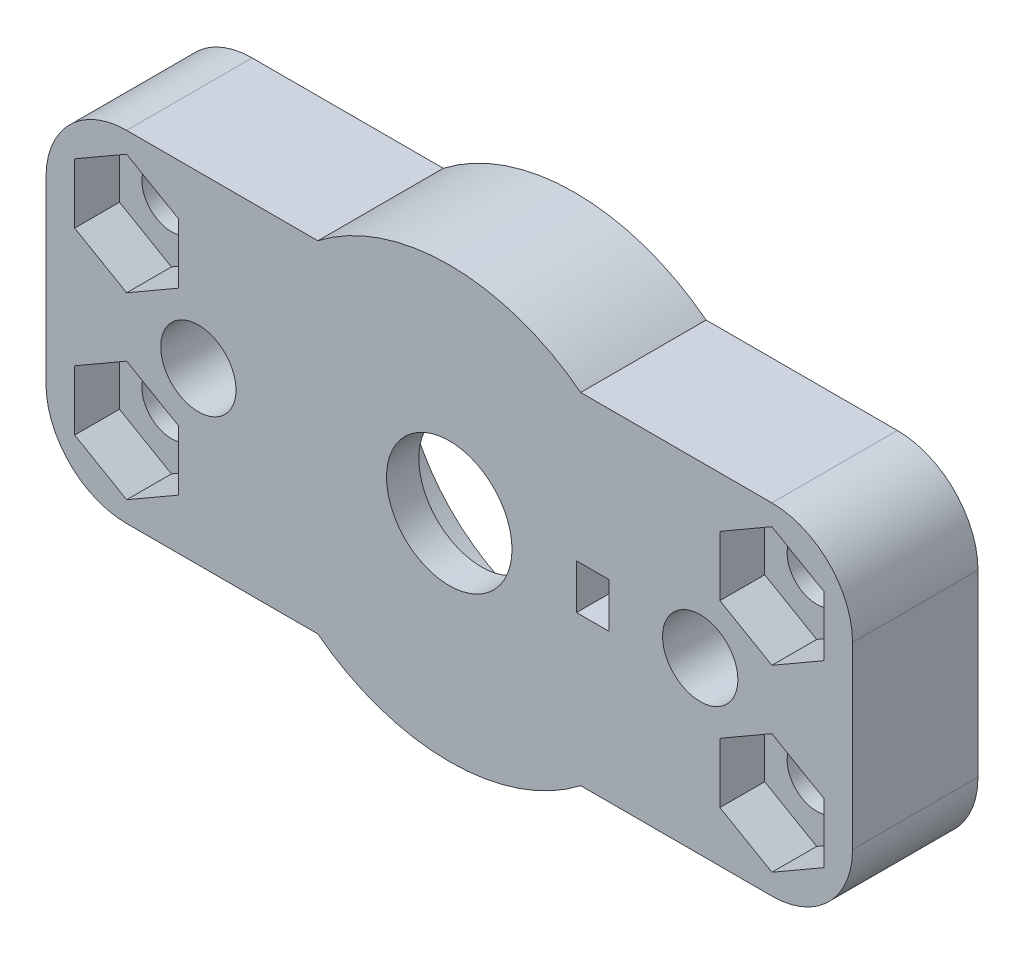
SolidWorks part; units mm, degrees
ref_plane "Front Plane" through (0, 0, 0) normal (0, 0, 1) x (1, 0, 0)
ref_plane "Top Plane" through (0, 0, 0) normal (0, 1, 0) x (1, 0, 0)
ref_plane "Right Plane" through (0, 0, 0) normal (1, 0, 0) x (0, 0, -1)
sketch "Sketch1" plane through (0, 0, 0) normal (0, 0, 1) x (1, 0, 0)
  circle A0 centre (0, 0) radius 9.5 construction
  circle A1 centre (0, 0) radius 2.5 construction
  dimension "D1" = 19
  dimension "D2" = 5
sketch "Sketch2" plane through (0, 0, 0) normal (0, 0, 1) x (1, 0, 0)
  line L0 (-18, 9.5) -> (-7.3314, 9.5)
  line L5 (0, 0) -> (0, 12) construction
  line L6 (0, 0) -> (-30.5723, 0) construction
  line L7 (-22.5, 5) -> (-22.5, -5)
  line L8 (22.5, 5) -> (22.5, -5)
  line L9 (18, 9.5) -> (7.3314, 9.5)
  line L10 (18, -9.5) -> (7.3314, -9.5)
  line L11 (-18, -9.5) -> (-7.3314, -9.5)
  arc A1 (-7.3314, 9.5) -> (7.3314, 9.5) centre (0, 0) cw
  circle A3 centre (0, 0) radius 9.5 construction
  arc A4 (-7.3314, -9.5) -> (7.3314, -9.5) centre (0, 0) ccw
  arc A5 (22.5, 5) -> (18, 9.5) centre (18, 5) ccw
  arc A6 (18, -9.5) -> (22.5, -5) centre (18, -5) ccw
  arc A7 (-22.5, -5) -> (-18, -9.5) centre (-18, -5) ccw
  arc A8 (-22.5, 5) -> (-18, 9.5) centre (-18, 5) cw
  circle A10 centre (-18, 5) radius 1.65
  circle A11 centre (18, 5) radius 1.65
  circle A12 centre (18, -5) radius 1.65
  circle A13 centre (-18, -5) radius 1.65
  point P0 (0, 0)
  point P8 (22.5, 9.5)
  point P21 (22.5, 0)
  point P22 (-22.5, 0)
  point P23 (22.5, -9.5)
  point P26 (-22.5, -9.5)
  point P29 (-22.5, 9.5)
  dimension "D1" = 2.5
  dimension "D2" = 4.5
  dimension "D3" = 3.3
  dimension "D4" = 10
  dimension "D5" = 45
extrude "Boss-Extrude1" add sketch "Sketch2" along normal blind 7
sketch "Sketch3" plane through (0, 0, 0) normal (0, 0, 1) x (1, 0, 0)
  circle A3 centre (0, 0) radius 9.7
  circle A4 centre (0, 0) radius 9.7
  dimension "D1" = 0.2
extrude "Cut-Extrude1" cut sketch "Sketch3" along normal blind 5
sketch "Sketch4" plane through (0, 0, 5) normal (0, 0, -1) x (-1, 0, 0)
  circle A0 centre (0, 0) radius 7.5
  dimension "D1" = 15
extrude "Cut-Extrude2" cut sketch "Sketch4" against normal blind 5
sketch "Sketch5" plane through (0, 0, 7) normal (0, 0, 1) x (1, 0, 0)
  line L0 (0, 0) -> (0, 12) construction
  line L1 (-18, 8.3486) -> (-20.9, 6.6743)
  line L2 (-20.9, 6.6743) -> (-20.9, 3.3257)
  line L3 (-20.9, 3.3257) -> (-18, 1.6514)
  line L4 (-18, 1.6514) -> (-15.1, 3.3257)
  line L5 (-15.1, 3.3257) -> (-15.1, 6.6743)
  line L6 (-15.1, 6.6743) -> (-18, 8.3486)
  line L7 (15.1, 6.6743) -> (18, 8.3486)
  line L8 (-22.5, 5) -> (-22.5, -5) construction
  line L9 (-22.5, 0) -> (0, 0) construction
  line L10 (15.1, 3.3257) -> (15.1, 6.6743)
  line L11 (18, 1.6514) -> (15.1, 3.3257)
  line L12 (20.9, 3.3257) -> (18, 1.6514)
  line L13 (20.9, 6.6743) -> (20.9, 3.3257)
  line L14 (18, 8.3486) -> (20.9, 6.6743)
  line L15 (15.1, -3.3257) -> (15.1, -6.6743)
  line L16 (18, -1.6514) -> (15.1, -3.3257)
  line L17 (20.9, -3.3257) -> (18, -1.6514)
  line L18 (20.9, -6.6743) -> (20.9, -3.3257)
  line L19 (18, -8.3486) -> (20.9, -6.6743)
  line L20 (15.1, -6.6743) -> (18, -8.3486)
  line L21 (-15.1, -6.6743) -> (-18, -8.3486)
  line L22 (-15.1, -3.3257) -> (-15.1, -6.6743)
  line L23 (-18, -1.6514) -> (-15.1, -3.3257)
  line L24 (-20.9, -3.3257) -> (-18, -1.6514)
  line L25 (-20.9, -6.6743) -> (-20.9, -3.3257)
  line L26 (-18, -8.3486) -> (-20.9, -6.6743)
  circle A0 centre (-18, 5) radius 2.9 construction
  arc A1 (7.3314, 9.5) -> (-7.3314, 9.5) centre (0, 0) ccw construction
  dimension "D1" = 5.8
extrude "Cut-Extrude3" cut sketch "Sketch5" against normal blind 2.5
sketch "Sketch6" plane through (0, 0, 7) normal (0, 0, 1) x (1, 0, 0)
  circle A0 centre (0, 0) radius 7.5
  circle A1 centre (0, 0) radius 7.5 construction
  circle A2 centre (0, 0) radius 3.5
  dimension "D1" = 7
extrude "Boss-Extrude2" add sketch "Sketch6" against normal blind 1.8
sketch "Sketch7" plane through (0, 0, 7) normal (0, 0, 1) x (1, 0, 0)
  line L0 (0, 0) -> (8, 0) construction
  line L2 (7.1, -1.25) -> (8.9, -1.25)
  line L3 (7.1, -1.25) -> (7.1, 1.25)
  line L4 (7.1, 1.25) -> (8.9, 1.25)
  line L5 (8.9, -1.25) -> (8.9, 1.25)
  line L6 (7.1, -1.25) -> (8.9, 1.25) construction
  line L7 (7.1, 1.25) -> (8.9, -1.25) construction
  dimension "D1" = 1.8
  dimension "D2" = 2.5
  dimension "D3" = 8
extrude "Cut-Extrude4" cut sketch "Sketch7" against normal blind 2.5
sketch "Sketch8" plane through (0, 0, 7) normal (0, 0, 1) x (1, 0, 0)
  line L0 (0, 0) -> (0, 12) construction
  circle A0 centre (-14, 0) radius 2.1
  arc A1 (7.3314, 9.5) -> (-7.3314, 9.5) centre (0, 0) ccw construction
  circle A2 centre (14, 0) radius 2.1
  dimension "D2" = 4.2
  dimension "D1" = 14
extrude "Cut-Extrude5" cut sketch "Sketch8" against normal blind 3
